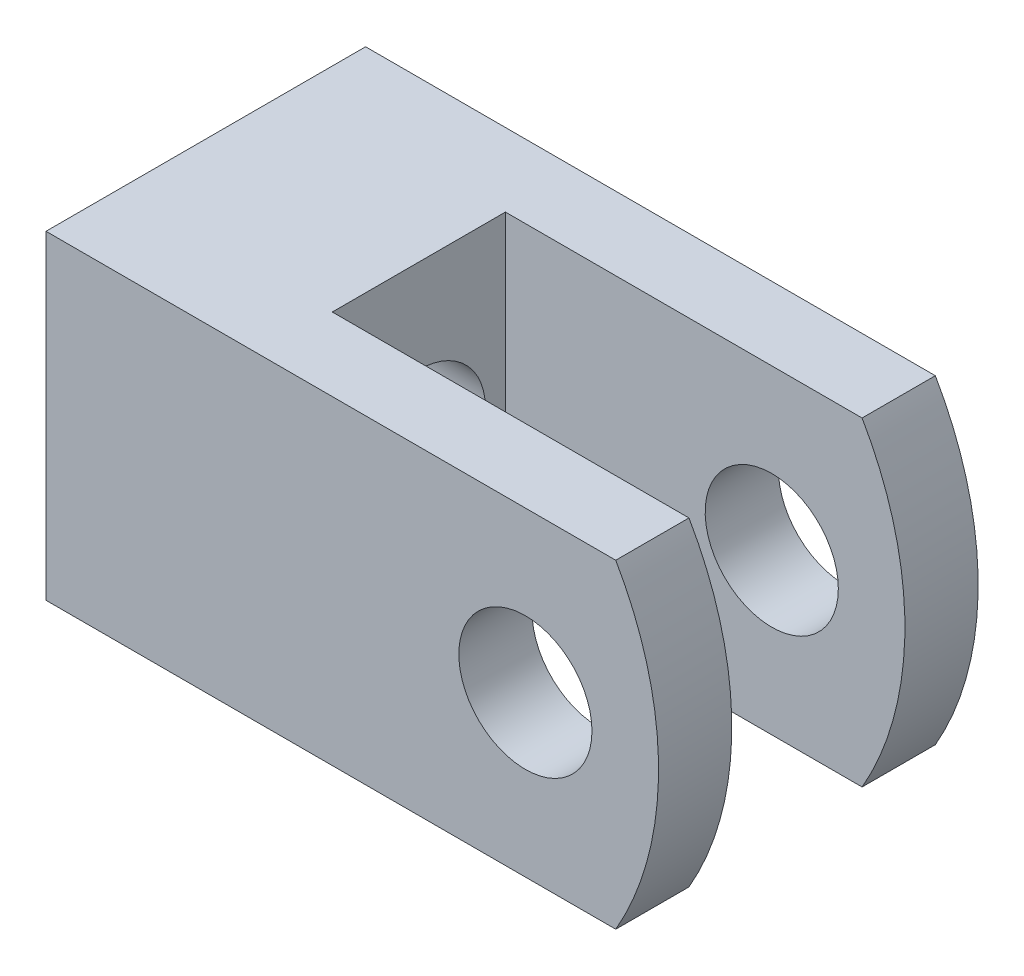
SolidWorks part; units mm, degrees
ref_plane "Front" through (0, 0, 0) normal (0, 0, 1) x (1, 0, 0)
ref_plane "Top" through (0, 0, 0) normal (0, 1, 0) x (1, 0, 0)
ref_plane "Right" through (0, 0, 0) normal (1, 0, 0) x (0, 0, -1)
sketch "Sketch2" plane through (0, 0, 0) normal (0, 0, 1) x (1, 0, 0)
  line L0 (-7, 0) -> (-7.053, 0) construction
  line L1 (-18, 6) -> (3.3923, 6)
  line L2 (-18, -6) -> (3.3923, -6)
  line L3 (-7, 0) -> (10.127, 0) construction
  line L4 (-18, 6) -> (-18, -6)
  arc A0 (3.3923, -6) -> (3.3923, 6) centre (-7, 0) ccw
  point P11 (5, 0)
  dimension "D1" = 24
  dimension "D2" = 12
  dimension "D3" = 5
  dimension "D4" = 18
extrude "Base-Extrude" add sketch "Sketch2" along normal mid plane 12
sketch "Sketch5" plane through (0, 0, 0) normal (1, 0, 0) x (0, 0, -1)
  line L0 (0, 0) -> (0, 10.22) construction
  line L1 (-6, 6) -> (6, 6) construction
  line L2 (-3.25, 6) -> (3.25, 6)
  line L3 (-3.25, 6) -> (-3.25, -6)
  line L4 (-3.25, -6) -> (3.25, -6)
  line L5 (3.25, 6) -> (3.25, -6)
  line L6 (-6, -6) -> (6, -6) construction
  dimension "D1" = 6.5
extrude "Cut-Extrude3" cut sketch "Sketch5" against normal blind 10 and the other way through all
sketch "Sketch6" plane through (0, 0, 0) normal (0, 0, 1) x (1, 0, 0)
  circle A0 centre (0, 0) radius 2.5
  dimension "D1" = 5
sketch "Sketch7" plane through (-18, 0, 0) normal (-1, 0, 0) x (0, 0, 1)
  circle A0 centre (0, 0) radius 2.5
  dimension "D1" = 5
extrude "Cut-Extrude4" cut sketch "Sketch7" against normal blind 11
chamfer "Chamfer2" distance 0.2 angle 45
extrude "Cut-Extrude5" cut sketch "Sketch6" against normal through all and the other way through all
